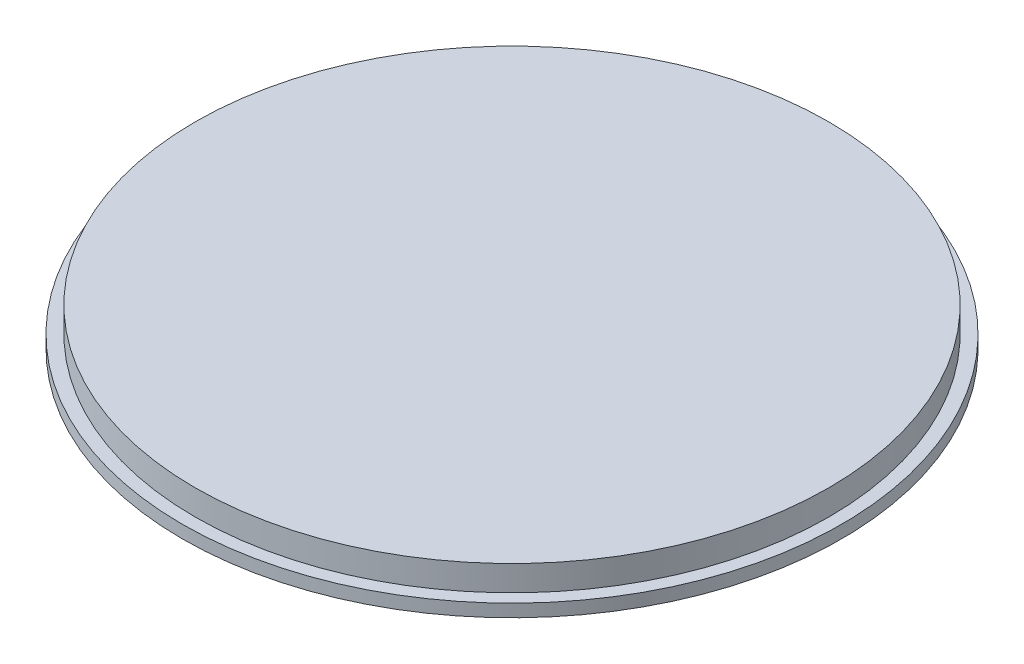
SolidWorks part; units mm, degrees
ref_plane "Front Plane" through (0, 0, 0) normal (0, 0, 1) x (1, 0, 0)
ref_plane "Top Plane" through (0, 0, 0) normal (0, 1, 0) x (1, 0, 0)
ref_plane "Right Plane" through (0, 0, 0) normal (1, 0, 0) x (0, 0, -1)
sketch "Sketch1" plane through (0, 0, 0) normal (0, 1, 0) x (1, 0, 0)
  circle A2 centre (0, 0) radius 26
  dimension "D1" = 52
extrude "Boss-Extrude4" add sketch "Sketch1" along normal blind 1
sketch "Sketch6" plane through (0, 1, 0) normal (0, 1, 0) x (1, 0, 0)
  circle A0 centre (0, 0) radius 25
  dimension "D1" = 50
extrude "Boss-Extrude5" add sketch "Sketch6" along normal blind 2
